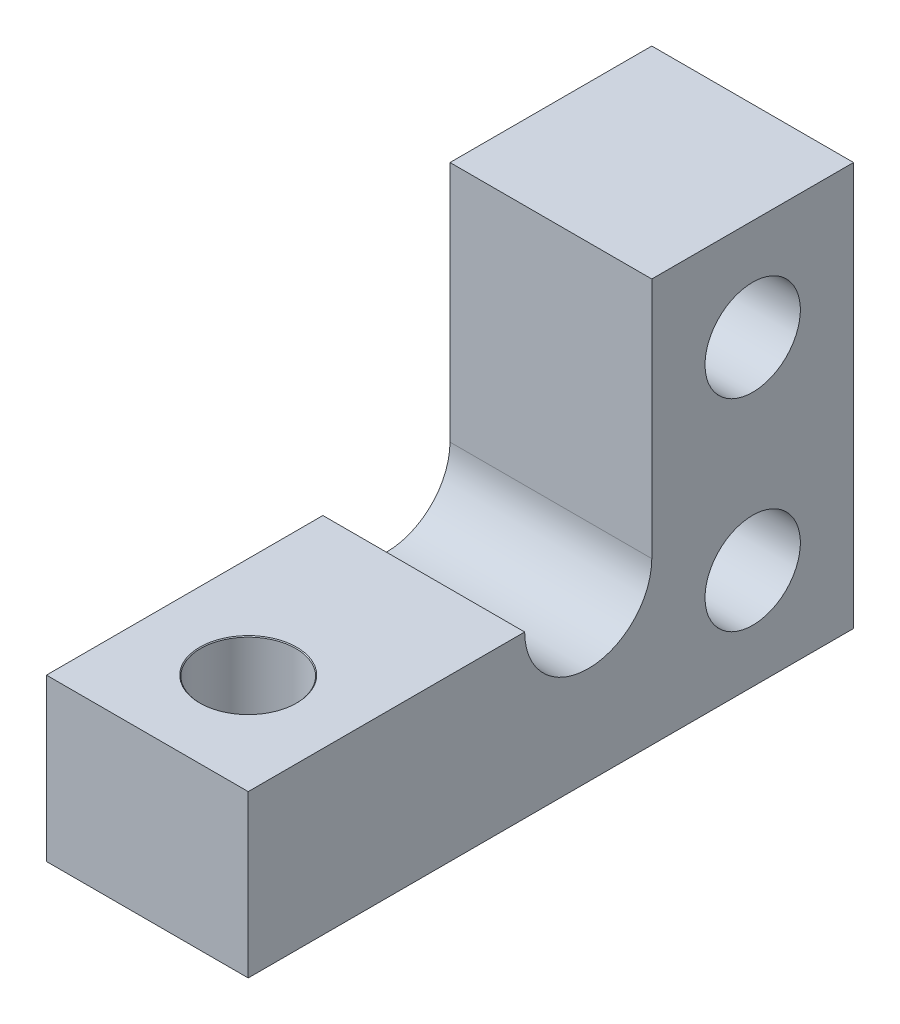
SolidWorks part; units mm, degrees
ref_plane "Front Plane" through (0, 0, 0) normal (0, 0, 1) x (1, 0, 0)
ref_plane "Top Plane" through (0, 0, 0) normal (0, 1, 0) x (1, 0, 0)
ref_plane "Right Plane" through (0, 0, 0) normal (1, 0, 0) x (0, 0, -1)
sketch "Sketch1" plane through (0, 0, 0) normal (1, 0, 0) x (0, 0, -1)
  line L1 (0, 0) -> (-19.05, 0)
  line L2 (-19.05, 0) -> (-19.05, 5.08)
  line L3 (-19.05, 5.08) -> (-6.35, 5.08)
  line L4 (-6.35, 5.08) -> (-6.35, 12.7)
  line L5 (-6.35, 12.7) -> (0, 12.7)
  line L6 (0, 12.7) -> (0, 0)
  line L7 (-3.175, 3.175) -> (-3.175, 9.525) construction
  circle A1 centre (-3.175, 9.525) radius 0.8469 construction
  circle A2 centre (-3.175, 3.175) radius 0.8469 construction
  circle A3 centre (-8.35, 5.08) radius 2
  point P14 (-3.175, 6.35)
  point P15 (0, 6.35)
  dimension "D5" = 6.35
  dimension "D3" = 4
  dimension "D8" = 1.6938
  dimension "D1" = 19.05
  dimension "D2" = 12.7
  dimension "D4" = 5.08
  dimension "D6" = 6.35
  dimension "D7" = 3.175
extrude "Boss-Extrude1" add sketch "Sketch1" along normal blind 6.35 contours A3 L3 L2 L1 L6 L5 L4
hole_wizard "Ø3.0mm Dowel Hole1" positions "Sketch2" profile "Sketch3" hole size "Ø3.0" standard "ANSI Metric" end condition through all
sketch "Sketch2" plane through (0, 0, 0) normal (-1, 0, 0) x (0, 0, 1)
  point P0 (3.175, 3.175)
  point P3 (3.175, 9.525)
sketch "Sketch3" plane through (0, 3.175, 3.175) normal (0, 1, 0) x (0, 0, 1)
  line L0 (0, 0) -> (0, 6.35)
  line L1 (0, 6.35) -> (1.5, 6.35)
  line L2 (1.5, 6.35) -> (1.5, 0.025)
  line L3 (1.5, 0.025) -> (1.525, 0)
  line L5 (1.525, 0) -> (0, 0)
  line L6 (-1.5, 0.025) -> (-1.525, 0) construction
  line L11 (0, -6.35) -> (0, 107.95) construction
  dimension "Thru Hole Dia." = 3
  dimension "Thru Hole Depth" = 6.35
  dimension "Near C'Sink Dia." = 3.05
  dimension "Near C'Sink Angle" = 90
sketch "Sketch4" plane through (0, 5.08, 0) normal (0, 1, 0) x (1, 0, 0)
  line L0 (0, -15.875) -> (6.35, -15.875) construction
  line L1 (0, 0) -> (0, -19.05) construction
  line L2 (6.35, -19.05) -> (6.35, -10.35) construction
  line L3 (6.35, -19.05) -> (0, -19.05) construction
  circle A0 centre (3.175, -15.875) radius 1.26
  dimension "D2" = 2.5199
  dimension "D1" = 3.175
hole_wizard "Ø3.0mm Dowel Hole2" positions "Sketch5" profile "Sketch6" hole size "Ø3.0" standard "ANSI Metric" end condition through all
sketch "Sketch5" plane through (0, 5.08, 0) normal (0, 1, 0) x (1, 0, 0)
  point P0 (3.175, -15.875)
sketch "Sketch6" plane through (3.175, 5.08, 15.875) normal (1, 0, 0) x (0, 0, 1)
  line L0 (0, 0) -> (0, 5.08)
  line L1 (0, 5.08) -> (1.5, 5.08)
  line L2 (1.5, 5.08) -> (1.5, 0.025)
  line L3 (1.5, 0.025) -> (1.525, 0)
  line L5 (1.525, 0) -> (0, 0)
  line L6 (-1.5, 0.025) -> (-1.525, 0) construction
  line L11 (0, -6.35) -> (0, 107.95) construction
  dimension "Thru Hole Dia." = 3
  dimension "Thru Hole Depth" = 5.08
  dimension "Near C'Sink Dia." = 3.05
  dimension "Near C'Sink Angle" = 90
